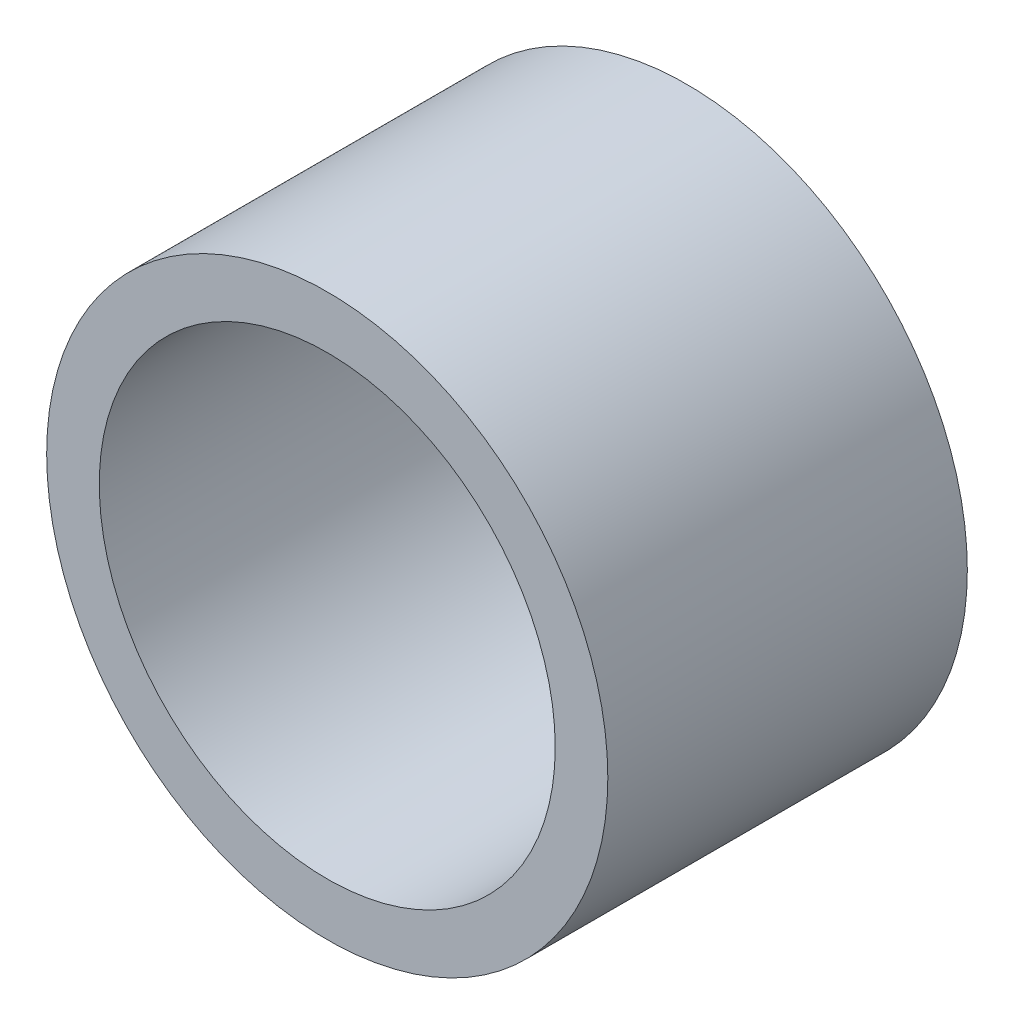
SolidWorks part; units mm, degrees
material "普通碳钢"
ref_plane "前视基准面" through (0, 0, 0) normal (0, 0, 1) x (1, 0, 0)
ref_plane "上视基准面" through (0, 0, 0) normal (0, 1, 0) x (1, 0, 0)
ref_plane "右视基准面" through (0, 0, 0) normal (1, 0, 0) x (0, 0, -1)
sketch "草图1" plane through (0, 0, 0) normal (0, 0, 1) x (1, 0, 0)
  circle A0 centre (0, 0) radius 13
  circle A1 centre (0, 0) radius 16
  dimension "D1" = 26
  dimension "D2" = 3
extrude "凸台-拉伸1" add sketch "草图1" along normal blind 20.5
